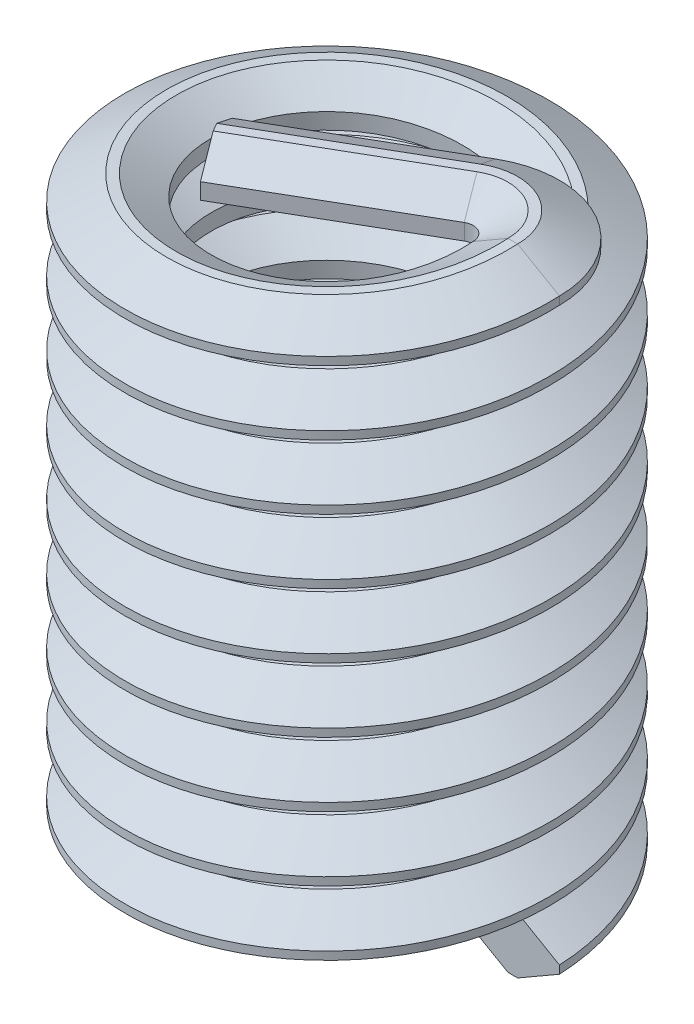
SolidWorks part; units mm, degrees
ref_plane "Front Plane" through (0, 0, 0) normal (0, 0, 1) x (1, 0, 0)
ref_plane "Top Plane" through (0, 0, 0) normal (0, 1, 0) x (1, 0, 0)
ref_plane "Right Plane" through (0, 0, 0) normal (1, 0, 0) x (0, 0, -1)
sketch "Sketch1" plane through (0, 0, 0) normal (0, 0, 1) x (-1, 0, 0)
  line L0 (0, 0) -> (0, 9.525) construction
  line L1 (-2.2126, 0) -> (-3.3125, 0.635) construction
  line L2 (-3.2286, 0.635) -> (-4.3285, 0) construction
  line L3 (-4.3285, 0) -> (-3.2286, -0.635) construction
  line L4 (-3.3125, -0.635) -> (-2.2126, 0) construction
  line L5 (-3.3125, -0.635) -> (-3.3125, 0.635) construction
  line L6 (-2.2126, 0) -> (0, 0) construction
  line L8 (-4.191, -0.0794) -> (-3.3661, -0.5556)
  line L9 (-3.175, -0.5556) -> (-2.4876, -0.1588)
  line L10 (-2.3501, -0.0794) -> (-2.3501, 0.0794) construction
  line L11 (-2.4876, 0.1588) -> (-3.175, 0.5556)
  line L12 (-3.3661, 0.5556) -> (-4.191, 0.0794)
  line L13 (-2.2126, 0) -> (-2.3501, 0) construction
  line L14 (-2.3501, 0) -> (-3.175, 0) construction
  line L15 (-3.3661, 0) -> (-4.191, 0) construction
  line L16 (-4.191, 0) -> (-4.3285, 0) construction
  line L17 (-3.3661, 0.5556) -> (-3.175, 0.5556)
  line L18 (-3.175, 0.5556) -> (-3.175, -0.5556) construction
  line L19 (-3.175, -0.5556) -> (-3.3661, -0.5556)
  line L20 (-3.3661, -0.5556) -> (-3.3661, 0.5556) construction
  line L21 (-3.3661, 0) -> (-3.3125, 0) construction
  line L22 (-3.3125, 0) -> (-3.175, 0) construction
  line L23 (-4.191, 0.635) -> (-4.191, -12.065) construction
  line L24 (-2.4876, -0.1588) -> (-2.4876, 0.1588)
  line L25 (-2.4876, 0) -> (-2.3501, 0) construction
  line L26 (-4.191, -0.0794) -> (-4.191, 0.0794)
  line L28 (4.191, 0.635) -> (4.191, -12.065) construction
  line L29 (-3.3125, -0.635) -> (-3.2286, -0.635) construction
  line L31 (-3.2286, 0.635) -> (-3.3125, 0.635) construction
  dimension "D3" = 1.27
  dimension "D4" = 0.1588
  dimension "Installed Length" = 12.7
  dimension "Thread Size" = 6.35
  dimension "Max OD" = 8.382
sketch "Sketch2" plane through (0, 0, 0) normal (0, 1, 0) x (1, 0, 0)
  circle A0 centre (0, 0) radius 3.175
curve "Helix/Spiral1" pitch 1.27 height 11.43 turns 9 parameters "Height"=11.43, "Pitch"=1.27
sweep "Sweep1" add profiles "Sketch1" path "Helix/Spiral1"
sketch "Sketch3" plane through (0, 0, 0) normal (0, 0, -1) x (-1, 0, 0)
  line L0 (-9.1748, 7.4104) -> (-2.2126, 11.43) construction
  line L1 (-5.3253, 13.2271) -> (-2.2126, 11.43) construction
  line L2 (-2.2126, 11.43) -> (-2.2126, 11.7475) construction
  line L8 (-3.175, 10.8744) -> (-2.4876, 11.2713)
  line L9 (-2.4876, 11.2713) -> (-2.4876, 11.5888)
  line L10 (-2.4876, 11.5888) -> (-3.175, 11.9856)
  line L12 (-3.3661, 11.9856) -> (-4.191, 11.5094)
  line L13 (-4.191, 11.5094) -> (-4.191, 11.3506)
  line L14 (-4.191, 11.3506) -> (-3.3661, 10.8744)
  line L16 (-3.175, 10.8744) -> (-2.4876, 11.2713)
  line L17 (-2.4876, 11.2713) -> (-2.4876, 11.5888)
  line L18 (-2.4876, 11.5888) -> (-3.175, 11.9856)
  line L20 (-3.3661, 11.9856) -> (-4.191, 11.5094)
  line L21 (-4.191, 11.5094) -> (-4.191, 11.3506)
  line L22 (-4.191, 11.3506) -> (-3.3661, 10.8744)
  line L23 (-3.175, 11.9856) -> (-3.3661, 11.9856)
  line L24 (-3.175, 11.9856) -> (-3.3661, 11.9856)
  line L25 (-3.3661, 10.8744) -> (-3.175, 10.8744)
  line L26 (-3.3661, 10.8744) -> (-3.175, 10.8744)
  dimension "D1" = 0
revolve "Revolve1" add sketch "Sketch3" angle 120 about L2
sketch "Sketch4" plane through (1.6595, 0, -0.9581) normal (-0.866, 0, 0.5) x (0.5, 0, 0.866)
  line L8 (-0.0472, 10.8744) -> (0.1439, 10.8744)
  line L9 (0.1439, 10.8744) -> (0.8314, 11.2713)
  line L10 (0.8314, 11.2713) -> (0.8314, 11.5888)
  line L11 (0.8314, 11.5888) -> (0.1439, 11.9856)
  line L12 (-0.0472, 10.8744) -> (0.1439, 10.8744)
  line L13 (-0.0472, 11.9856) -> (-0.8721, 11.5094)
  line L14 (-0.8721, 11.5094) -> (-0.8721, 11.3506)
  line L15 (-0.8721, 11.3506) -> (-0.0472, 10.8744)
  line L17 (0.1439, 10.8744) -> (0.8314, 11.2713)
  line L18 (0.8314, 11.2713) -> (0.8314, 11.5888)
  line L19 (0.8314, 11.5888) -> (0.1439, 11.9856)
  line L21 (-0.0472, 11.9856) -> (-0.8721, 11.5094)
  line L22 (-0.8721, 11.5094) -> (-0.8721, 11.3506)
  line L23 (-0.8721, 11.3506) -> (-0.0472, 10.8744)
  spline S4 degree 1 poles (2000.1308, 11.9856) (-2000.0363, 11.9856) knots -10465.064272 -10465.064272 10466.076373 10466.076373 only from (0.1439, 11.9856) to (-0.0472, 11.9856)
  spline S5 degree 1 poles (0.1439, 11.9856) (-0.0472, 11.9856) knots 0 0 1 1
  dimension "D1" = 0
extrude "Extrude1" add sketch "Sketch4" along normal blind 3.81
sketch "Sketch5" plane through (0, 0, 0) normal (0, 1, 0) x (1, 0, 0)
  line L0 (-1.6637, -0.9061) -> (1.6359, 0.9989) construction
  circle A0 centre (-0.0139, 0.0464) radius 4.6608
equation "\"D3@Sketch1\" = \"Pitch@Helix/Spiral1\""
equation "\"D4@Sketch1\" = \"D3@Sketch1\"  * 1 / 8"
equation "\"D1@Extrude1\" = \"Thread Size@Sketch1\" * 0.6"
equation "\"Height@Helix/Spiral1\" = \"Installed Length@Sketch1\" - \"Pitch@Helix/Spiral1\""
